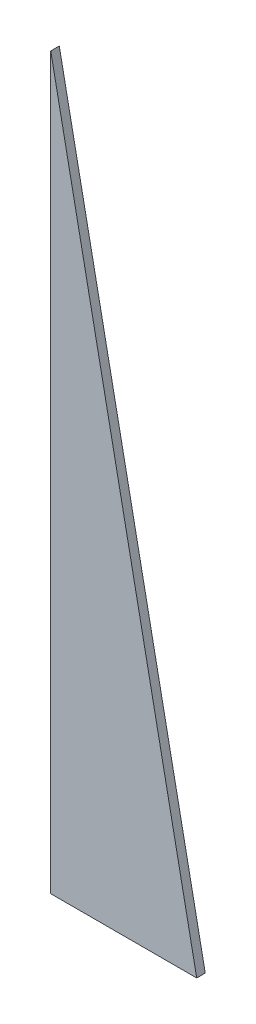
SolidWorks part; units mm, degrees
ref_plane "Front Plane" through (0, 0, 0) normal (0, 0, 1) x (1, 0, 0)
ref_plane "Top Plane" through (0, 0, 0) normal (0, 1, 0) x (1, 0, 0)
ref_plane "Right Plane" through (0, 0, 0) normal (1, 0, 0) x (0, 0, -1)
sketch "Sketch1" plane through (0, 0, 0) normal (0, 0, 1) x (1, 0, 0)
  line L3 (-531.6807, -144.416) -> (-531.6807, -315.416)
  line L4 (-531.6807, -315.416) -> (-497.4807, -315.416)
  line L5 (-497.4807, -315.416) -> (-531.6807, -144.416)
  dimension "D1" = 34.2
  dimension "D2" = 171
extrude "Boss-Extrude1" add sketch "Sketch1" along normal blind 2
